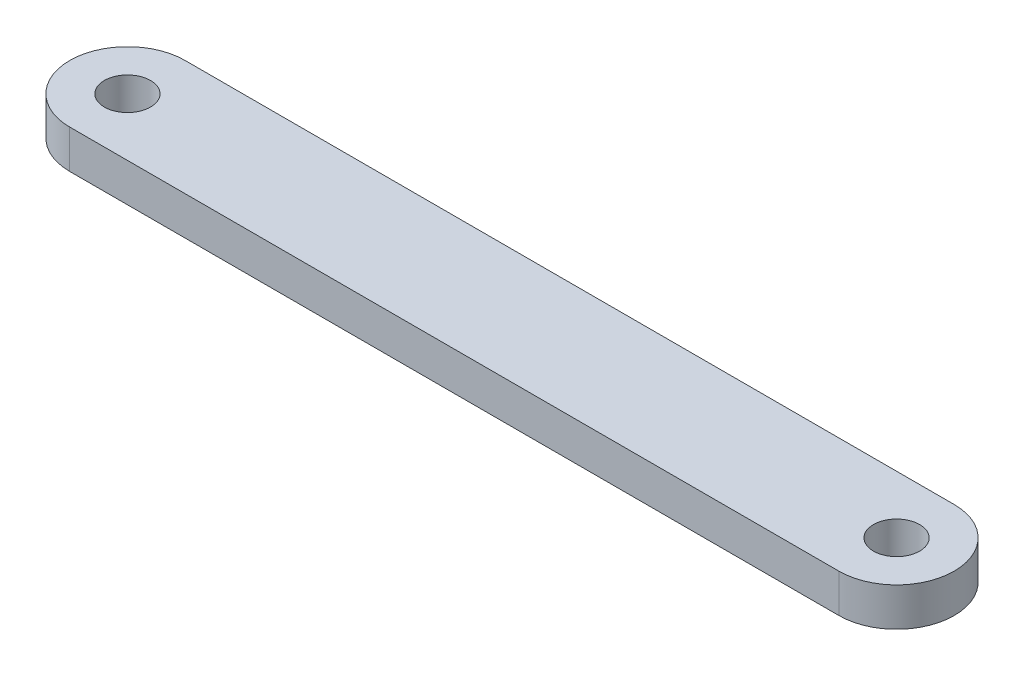
SolidWorks part; units mm, degrees
ref_plane "Front Plane" through (0, 0, 0) normal (0, 0, 1) x (1, 0, 0)
ref_plane "Top Plane" through (0, 0, 0) normal (0, 1, 0) x (1, 0, 0)
ref_plane "Right Plane" through (0, 0, 0) normal (1, 0, 0) x (0, 0, -1)
sketch "Sketch1" plane through (0, 0, 0) normal (0, 1, 0) x (1, 0, 0)
  line L0 (0, 7.5) -> (100, 7.5)
  line L1 (0, -7.5) -> (100, -7.5)
  arc A0 (0, 7.5) -> (0, -7.5) centre (0, 0) ccw
  arc A1 (100, -7.5) -> (100, 7.5) centre (100, 0) ccw
  circle A2 centre (100, 0) radius 3
  circle A3 centre (0, 0) radius 3
  point P8 (0, 0)
  dimension "D1" = 15
  dimension "D3" = 6
  dimension "D4" = 6
  dimension "D2" = 100
extrude "Boss-Extrude1" add sketch "Sketch1" along normal blind 5
